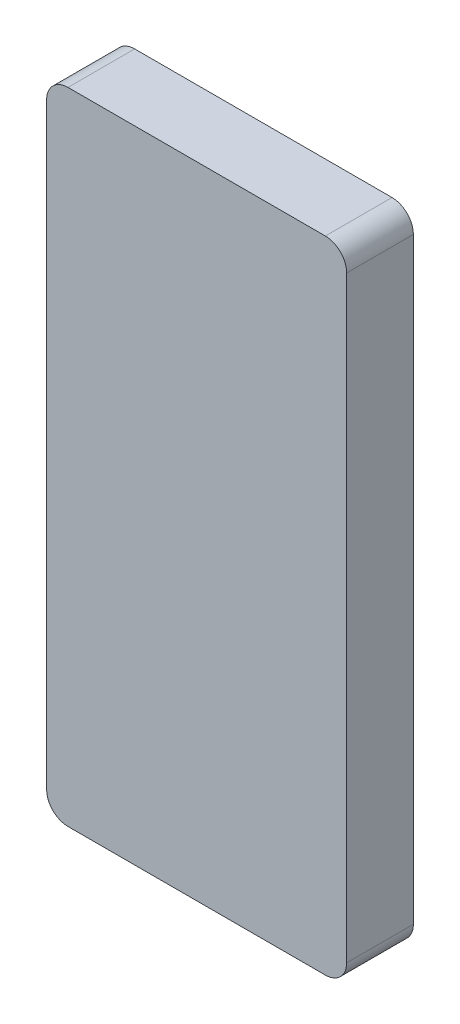
SolidWorks part; units mm, degrees
ref_plane "Front Plane" through (0, 0, 0) normal (0, 0, 1) x (1, 0, 0)
ref_plane "Top Plane" through (0, 0, 0) normal (0, 1, 0) x (1, 0, 0)
ref_plane "Right Plane" through (0, 0, 0) normal (1, 0, 0) x (0, 0, -1)
sketch "Sketch2" plane through (0, 0, 0) normal (0, 0, 1) x (1, 0, 0)
  line L1 (-30.6387, 76.2) -> (30.6387, 76.2)
  line L2 (-35.7188, 71.12) -> (-35.7187, -71.12)
  line L3 (-30.6387, -76.2) -> (30.6387, -76.2)
  line L4 (35.7188, 71.12) -> (35.7188, -71.12)
  line L5 (-35.7188, 76.2) -> (35.7188, -76.2) construction
  line L6 (-35.7187, -76.2) -> (35.7188, 76.2) construction
  arc A0 (-30.6387, 76.2) -> (-35.7188, 71.12) centre (-30.6387, 71.12) ccw
  arc A1 (30.6387, 76.2) -> (35.7188, 71.12) centre (30.6387, 71.12) cw
  arc A2 (30.6387, -76.2) -> (35.7188, -71.12) centre (30.6388, -71.12) ccw
  arc A3 (-35.7187, -71.12) -> (-30.6387, -76.2) centre (-30.6387, -71.12) ccw
  point P0 (0, 0)
  dimension "D3" = 5.08
  dimension "D1" = 152.4
  dimension "D2" = 71.4375
extrude "Boss-Extrude1" add sketch "Sketch2" along normal blind 15.875
